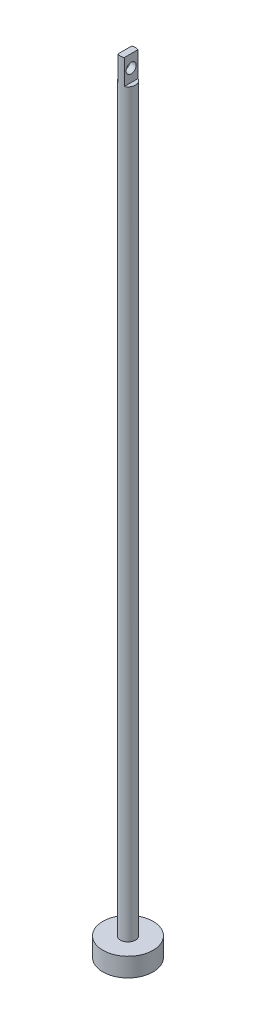
SolidWorks part; units mm, degrees
ref_plane "前视基准面" through (0, 0, 0) normal (0, 0, 1) x (1, 0, 0)
ref_plane "上视基准面" through (0, 0, 0) normal (0, 1, 0) x (1, 0, 0)
ref_plane "右视基准面" through (0, 0, 0) normal (1, 0, 0) x (0, 0, -1)
sketch "草图1" plane through (0, 0, 0) normal (0, 1, 0) x (1, 0, 0)
  circle A0 centre (0, 0) radius 20
  dimension "D1" = 40
extrude "凸台-拉伸1" add sketch "草图1" along normal blind 15
sketch "草图2" plane through (0, 15, 0) normal (0, 1, 0) x (1, 0, 0)
  circle A0 centre (0, 0) radius 6
  dimension "D1" = 12
extrude "凸台-拉伸2" add sketch "草图2" along normal blind 610
sketch "草图3" plane through (0, 625, 0) normal (0, 1, 0) x (1, 0, 0)
  line L1 (-2.5, 10) -> (2.5, 10)
  line L2 (-2.5, 10) -> (-2.5, -10)
  line L3 (-2.5, -10) -> (2.5, -10)
  line L4 (2.5, 10) -> (2.5, -10)
  line L5 (-2.5, 10) -> (2.5, -10) construction
  line L6 (-2.5, -10) -> (2.5, 10) construction
  point P0 (0, 0)
  point P1 (0, 0)
  dimension "D1" = 5
  dimension "D2" = 20
extrude "切除-拉伸1" cut sketch "草图3" against normal blind 20 flip side to cut
ref_plane "基准面1" through (-2.5, 0, 0) normal (-1, 0, 0) x (0, 0, 1)
sketch "草图4" plane through (-2.5, 0, 0) normal (-1, 0, 0) x (0, 0, 1)
  line L0 (0, 0) -> (0, 362.7684) construction
  line L4 (-5.4544, 615) -> (5.4544, 615)
  line L5 (-5.4544, 615) -> (5.4544, 615) construction
  circle A0 centre (0, 615) radius 4
  point P8 (0, 615)
  dimension "D2" = 8
  dimension "D1" = 10
extrude "切除-拉伸2" cut sketch "草图4" against normal blind 20
